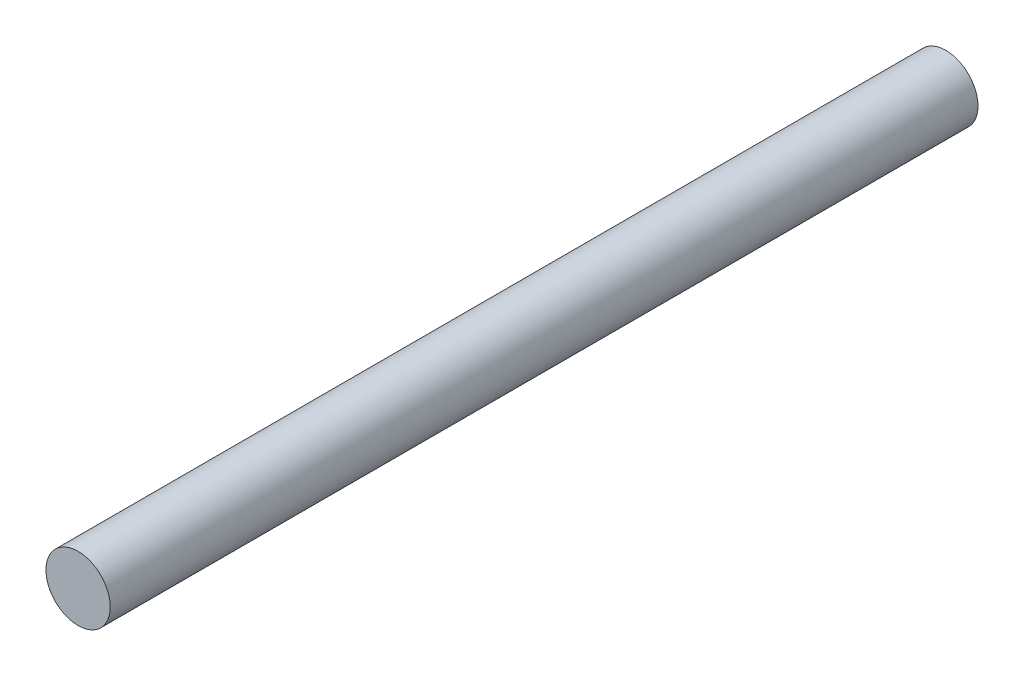
SolidWorks part; units mm, degrees
ref_plane "Front Plane" through (0, 0, 0) normal (0, 0, 1) x (1, 0, 0)
ref_plane "Top Plane" through (0, 0, 0) normal (0, 1, 0) x (1, 0, 0)
ref_plane "Right Plane" through (0, 0, 0) normal (1, 0, 0) x (0, 0, -1)
sketch "Sketch1" plane through (0, 0, 0) normal (0, 0, 1) x (1, 0, 0)
  circle A0 centre (0, 0) radius 4
  dimension "D1" = 8
extrude "Boss-Extrude1" add sketch "Sketch1" along normal blind 107.95
